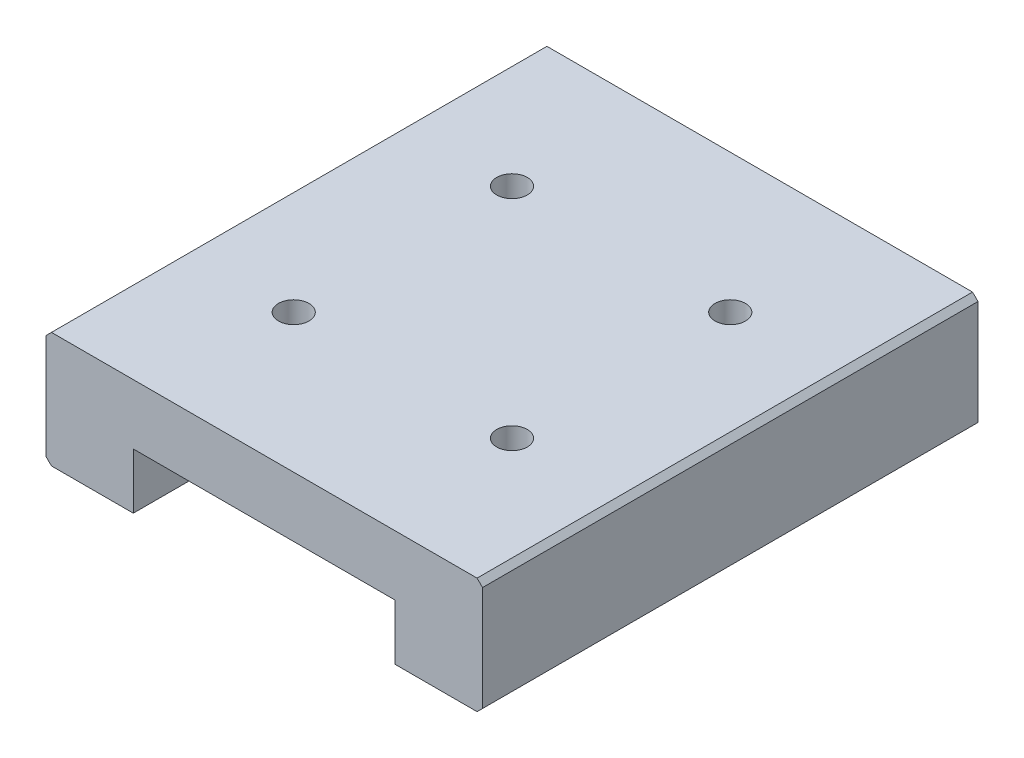
SolidWorks part; units mm, degrees
ref_plane "前视基准面" through (0, 0, 0) normal (0, 0, 1) x (1, 0, 0)
ref_plane "上视基准面" through (0, 0, 0) normal (0, 1, 0) x (1, 0, 0)
ref_plane "右视基准面" through (0, 0, 0) normal (1, 0, 0) x (0, 0, -1)
sketch "草图1" plane through (0, 0, 0) normal (0, 0, 1) x (1, 0, 0)
  line L0 (-17.8228, 1.9051) -> (-17.8228, -3.1949) construction
  line L1 (-25.3228, 7.4051) -> (13.6772, 7.4051)
  line L2 (-25.8228, 6.9051) -> (-25.8228, -2.6949)
  line L3 (-25.3228, -3.1949) -> (-17.8228, -3.1949)
  line L4 (14.1772, 6.9051) -> (14.1772, -2.6949)
  line L5 (6.1772, 1.9051) -> (6.1772, -3.1949) construction
  line L6 (-25.8228, 6.9051) -> (-25.3228, 7.4051)
  line L7 (-17.8228, -3.1949) -> (-17.8228, 1.9051)
  line L8 (-17.8228, 1.9051) -> (6.1772, 1.9051)
  line L9 (6.1772, 1.9051) -> (6.1772, -3.1949)
  line L10 (6.1772, -3.1949) -> (13.6772, -3.1949)
  line L11 (-17.8228, 1.9051) -> (6.1772, 1.9051) construction
  line L12 (-25.8228, -2.6949) -> (-25.3228, -3.1949)
  line L13 (13.6772, -3.1949) -> (14.1772, -2.6949)
  line L14 (13.6772, 7.4051) -> (14.1772, 6.9051)
  point P0 (-25.8228, 7.4051)
  point P1 (14.1772, -3.1949)
  point P2 (-25.8228, -3.1949)
  point P3 (14.1772, 7.4051)
  dimension "D1" = 40
  dimension "D2" = 10.6
  dimension "D3" = 8
  dimension "D4" = 8
extrude "凸台-拉伸1" add sketch "草图1" along normal blind 45.4 contours L1 L14 L4 L13 L10 L9 L8 L7 L3 L12 L2 L6
sketch "草图2" plane through (0, 7.4051, 0) normal (0, 1, 0) x (1, 0, 0)
  line L0 (13.6772, -22.7) -> (-25.3228, -22.7) construction
  line L1 (13.6772, -45.4) -> (13.6772, 0) construction
  line L2 (-25.3228, -45.4) -> (-25.3228, 0) construction
  line L3 (26.3595, -12.7) -> (-32.4605, -12.7) construction
  line L4 (27.8474, -32.7) -> (-32.4605, -32.7) construction
  line L5 (-5.8228, 0) -> (-5.8228, -45.4) construction
  line L6 (-25.3228, 0) -> (13.6772, 0) construction
  line L7 (-25.3228, -45.4) -> (13.6772, -45.4) construction
  line L8 (4.1772, 13.849) -> (4.1772, -58.5092)
  line L9 (-15.8228, 11.5303) -> (-15.8228, -53.57)
  dimension "D1" = 10
  dimension "D2" = 10
  dimension "D3" = 10
  dimension "D4" = 10
hole_wizard "孔1" positions "3D草图1" profile "草图3" legacy
sketch3d "3D草图1"
  line L0 (4.1772, 7.4051, -13.849) -> (4.1772, 7.4051, 58.5092) construction
  line L1 (26.3595, 7.4051, 12.7) -> (-32.4605, 7.4051, 12.7) construction
  line L2 (27.8474, 7.4051, 32.7) -> (-32.4605, 7.4051, 32.7) construction
  line L3 (-15.8228, 7.4051, -11.5303) -> (-15.8228, 7.4051, 53.57) construction
  point P0 (4.1772, 7.4051, 12.7)
  point P6 (4.1772, 7.4051, 32.7)
  point P10 (-15.8228, 7.4051, 12.7)
  point P14 (-15.8228, 7.4051, 32.7)
sketch "草图3" plane through (4.1772, 7.4051, 12.7) normal (1, 0, 0) x (0, 0, 1)
  line L0 (0, 0) -> (0, 3.5)
  line L1 (0, 3.5) -> (1.4, 3.5)
  line L2 (1.4, 3.5) -> (1.4, 0)
  line L3 (1.4, 0) -> (0, 0)
  line L4 (0, 110) -> (0, -10) construction
  dimension "直径" = 2.8
  dimension "深度" = 3.5
